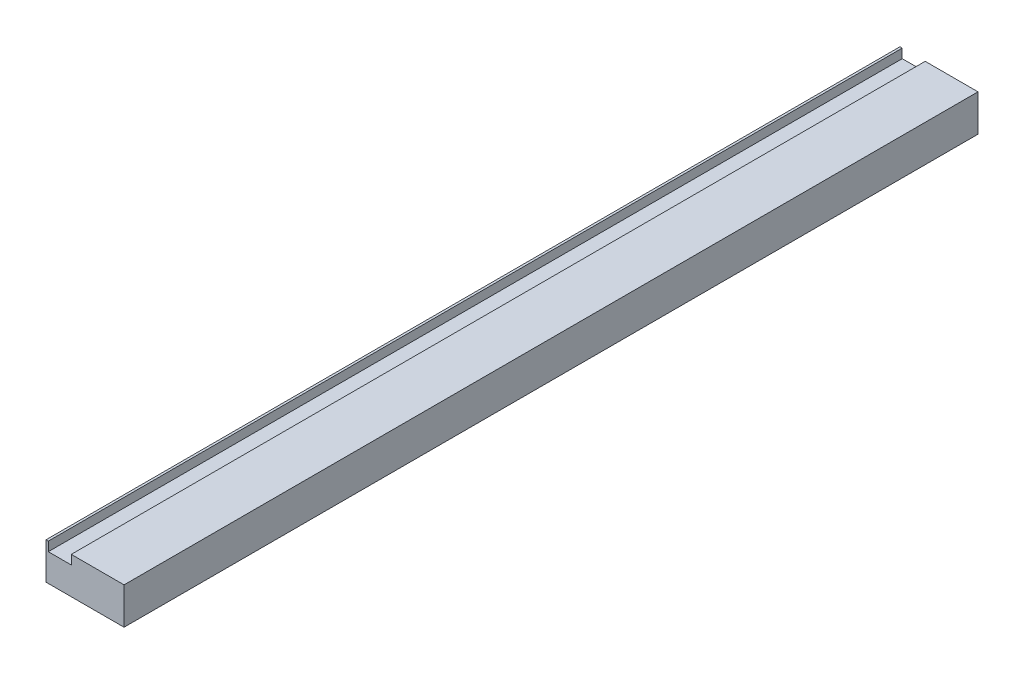
SolidWorks part; units mm, degrees
ref_plane "Front Plane" through (0, 0, 0) normal (0, 0, 1) x (1, 0, 0)
ref_plane "Top Plane" through (0, 0, 0) normal (0, 1, 0) x (1, 0, 0)
ref_plane "Right Plane" through (0, 0, 0) normal (1, 0, 0) x (0, 0, -1)
sketch "Sketch1" plane through (0, 0, 0) normal (0, 1, 0) x (1, 0, 0)
  line L1 (-7.5, -232.5) -> (7.5, -232.5)
  line L2 (-7.5, -232.5) -> (-7.5, 232.5)
  line L3 (-7.5, 232.5) -> (7.5, 232.5)
  line L4 (7.5, -232.5) -> (7.5, 232.5)
  line L5 (-7.5, -232.5) -> (7.5, 232.5) construction
  line L6 (-7.5, 232.5) -> (7.5, -232.5) construction
  point P0 (0, 0)
extrude "Boss-Extrude1" add sketch "Sketch1" along normal blind 20
sketch "Sketch2" plane through (0, 20, 0) normal (0, 1, 0) x (1, 0, 0)
  line L1 (-6.25, -232.5) -> (6.25, -232.5)
  line L2 (-6.25, -232.5) -> (-6.25, 232.5)
  line L3 (-6.25, 232.5) -> (6.25, 232.5)
  line L4 (6.25, -232.5) -> (6.25, 232.5)
  line L5 (-6.25, -232.5) -> (6.25, 232.5) construction
  line L6 (-6.25, 232.5) -> (6.25, -232.5) construction
  point P0 (0, 0)
extrude "Cut-Extrude1" cut sketch "Sketch2" against normal blind 5
sketch "Sketch4" plane through (7.5, 0, 0) normal (-1, 0, 0) x (0, 0, 1)
  line L1 (-232.5, 20) -> (232.5, 20)
  line L2 (-232.5, 20) -> (-232.5, 0)
  line L3 (-232.5, 0) -> (232.5, 0)
  line L4 (232.5, 20) -> (232.5, 0)
extrude "Boss-Extrude3" add sketch "Sketch4" against normal blind 27.5
